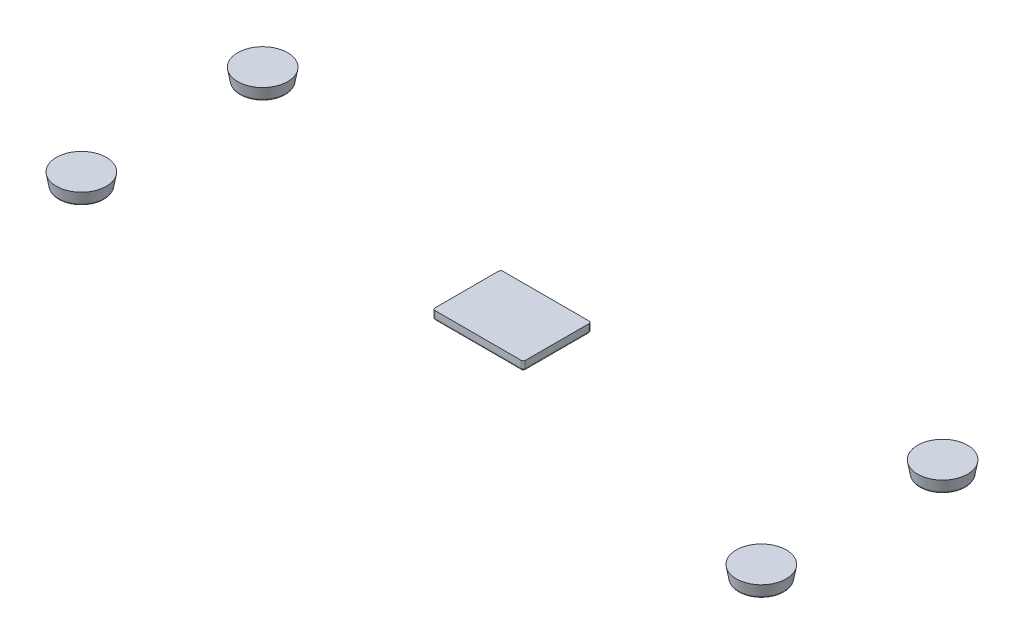
SolidWorks part; units mm, degrees
material "Rubber"
ref_plane "Front Plane" through (0, 0, 0) normal (0, 0, 1) x (1, 0, 0)
ref_plane "Top Plane" through (0, 0, 0) normal (0, 1, 0) x (1, 0, 0)
ref_plane "Right Plane" through (0, 0, 0) normal (1, 0, 0) x (0, 0, -1)
sketch "Sketch1" plane through (0, 0, 0) normal (0, 1, 0) x (1, 0, 0)
  line L1 (-75, 20) -> (75, 20) construction
  line L2 (-75, 20) -> (-75, -20) construction
  line L3 (-75, -20) -> (75, -20) construction
  line L4 (75, 20) -> (75, -20) construction
  line L5 (-75, 20) -> (75, -20) construction
  line L6 (-75, -20) -> (75, 20) construction
  circle A0 centre (-75, 20) radius 5
  circle A1 centre (-75, -20) radius 5
  circle A2 centre (75, 20) radius 5
  circle A3 centre (75, -20) radius 5
  point P0 (0, 0)
  dimension "D1" = 10
  dimension "D2" = 40
  dimension "D3" = 150
extrude "Boss-Extrude1" add sketch "Sketch1" along normal blind 2.95 draft 10 draft outward yes
fillet "Fillet1" radius 0.5 1 edges at (-75, 0, -15)
fillet "Fillet2" radius 0.5 1 edges at (-75, 0, 25)
fillet "Fillet3" radius 0.5 1 edges at (75, 0, -15)
fillet "Fillet4" radius 0.5 1 edges at (75, 0, 25)
sketch "Sketch2" plane through (0, 2.95, 0) normal (0, 1, 0) x (1, 0, 0)
  line L1 (-10, 7.5) -> (10, 7.5)
  line L2 (-10, 7.5) -> (-10, -7.5)
  line L3 (-10, -7.5) -> (10, -7.5)
  line L4 (10, 7.5) -> (10, -7.5)
  line L5 (-10, 7.5) -> (10, -7.5) construction
  line L6 (-10, -7.5) -> (10, 7.5) construction
  point P0 (0, 0)
  dimension "D1" = 15
  dimension "D2" = 20
extrude "Boss-Extrude2" add sketch "Sketch2" against normal blind 2 separate body
fillet "Fillet5" radius 0.5 4 edges at (-10, 1.95, -7.5) (-10, 1.95, 7.5) (10, 1.95, 7.5) (10, 1.95, -7.5)
fillet "Fillet6" radius 0.5 8 edges at (-9.8536, 0.95, 7.3536) (-10, 0.95, 0) (-9.8536, 0.95, -7.3536) (0, 0.95, -7.5) (9.8536, 0.95, -7.3536) (10, 0.95, 0) (9.8536, 0.95, 7.3536) (0, 0.95, 7.5)
